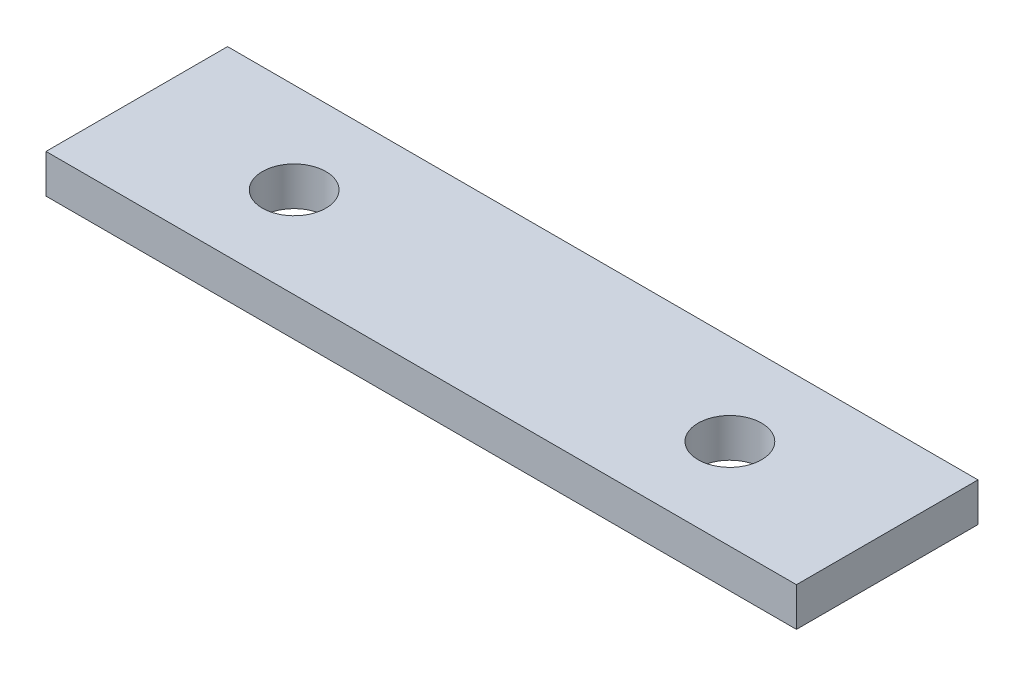
SolidWorks part; units mm, degrees
ref_plane "Front Plane" through (0, 0, 0) normal (0, 0, 1) x (1, 0, 0)
ref_plane "Top Plane" through (0, 0, 0) normal (0, 1, 0) x (1, 0, 0)
ref_plane "Right Plane" through (0, 0, 0) normal (1, 0, 0) x (0, 0, -1)
sketch "Sketch1" plane through (0, 0, 0) normal (0, 1, 0) x (1, 0, 0)
  line L1 (-31, 7.5) -> (31, 7.5)
  line L2 (-31, 7.5) -> (-31, -7.5)
  line L3 (-31, -7.5) -> (31, -7.5)
  line L4 (31, 7.5) -> (31, -7.5)
  line L5 (-31, 7.5) -> (31, -7.5) construction
  line L6 (-31, -7.5) -> (31, 7.5) construction
  point P0 (0, 0)
  dimension "D1" = 62
  dimension "D2" = 15
extrude "Boss-Extrude1" add sketch "Sketch1" along normal blind 3.2
sketch "Sketch2" plane through (0, 3.2, 0) normal (0, 1, 0) x (1, 0, 0)
  line L0 (31, -7.5) -> (31, 7.5) construction
  line L1 (-31, 7.5) -> (-31, -7.5) construction
  line L2 (-31, -7.5) -> (31, -7.5) construction
  circle A0 centre (-18, 0) radius 2.625
  circle A1 centre (18, 0) radius 2.625
  dimension "D1" = 5.25
  dimension "D2" = 5.25
  dimension "D3" = 13
  dimension "D4" = 13
  dimension "D5" = 7.5
extrude "Cut-Extrude1" cut sketch "Sketch2" against normal up to next
